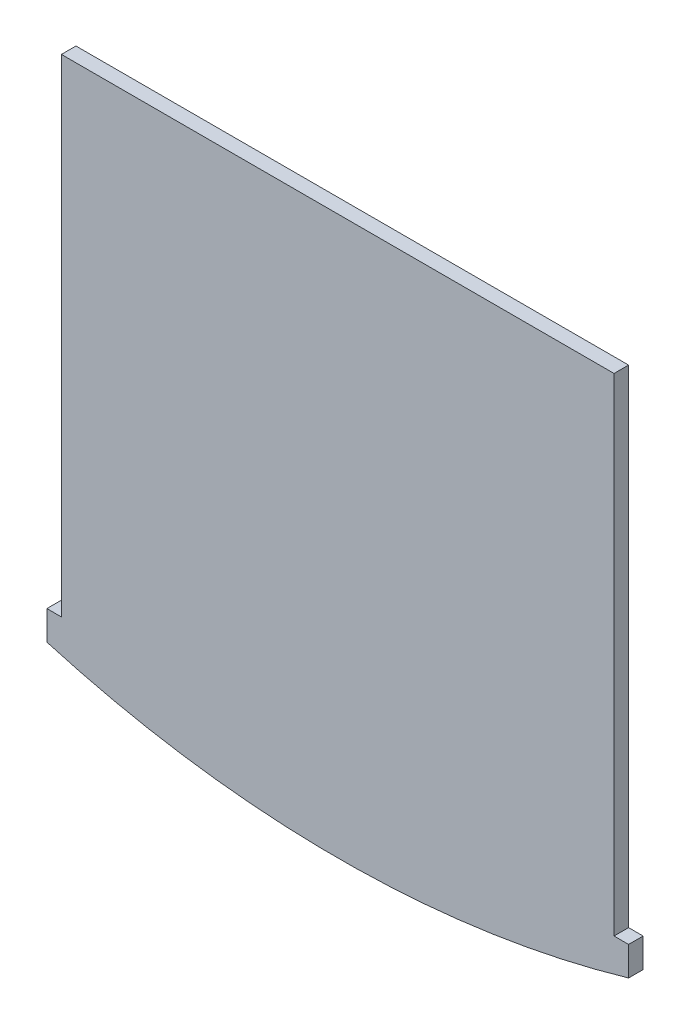
SolidWorks part; units mm, degrees
ref_plane "Front Plane" through (0, 0, 0) normal (0, 0, 1) x (1, 0, 0)
ref_plane "Top Plane" through (0, 0, 0) normal (0, 1, 0) x (1, 0, 0)
ref_plane "Right Plane" through (0, 0, 0) normal (1, 0, 0) x (0, 0, -1)
sketch "Sketch2" plane through (0, 0, 0) normal (0, 0, 1) x (1, 0, 0)
  line L3 (38, 0) -> (-38, 0)
  line L4 (-38, 0) -> (-38, -67)
  line L5 (38, 0) -> (38, -67)
  line L6 (-40, -67) -> (-38, -67)
  line L7 (38, -67) -> (40, -67)
  line L8 (0, 49.9528) -> (0, -103.3181) construction
  line L9 (-40, -67) -> (-40, -71)
  line L10 (40, -67) -> (40, -71)
  arc A2 (-40, -71) -> (40, -71) centre (0, 66.2917) ccw
  point P13 (0, 0)
  point P14 (0, 0)
  point P15 (0, 0)
  point P16 (40, -69.49)
  point P17 (0, -103.3181)
  dimension "D3" = 2
  dimension "D1" = 4
  dimension "D2" = 76
  dimension "D4" = 67
  dimension "D6" = 38
extrude "Boss-Extrude1" add sketch "Sketch2" along normal blind 2
